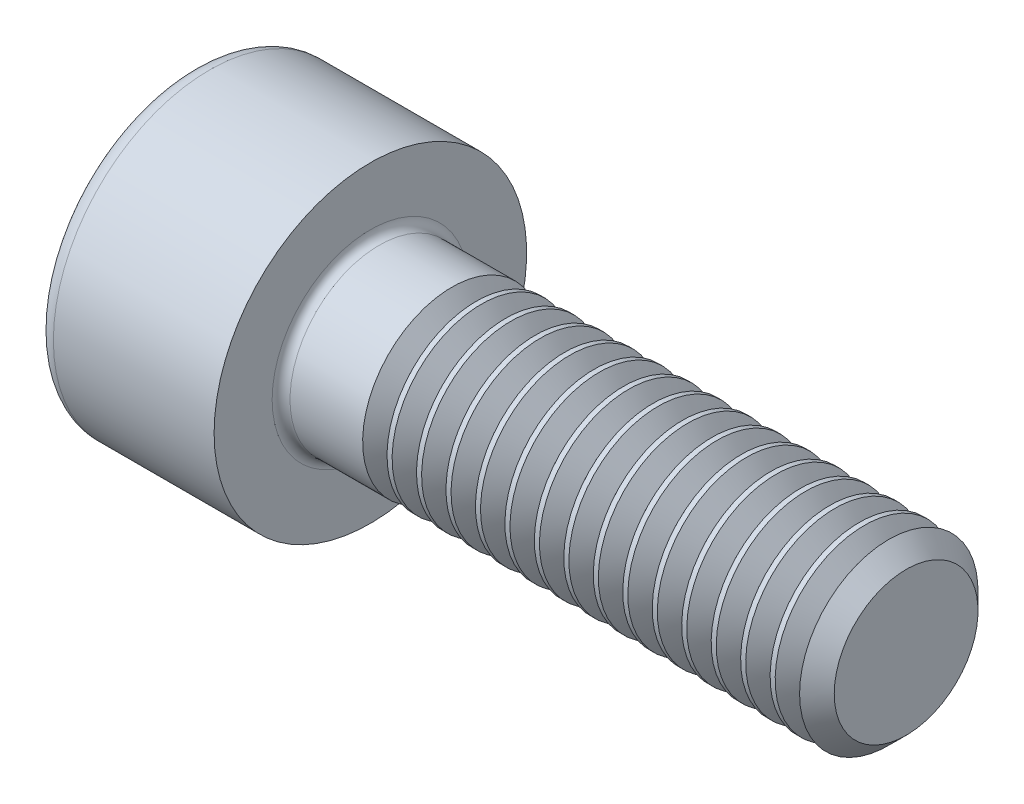
SolidWorks part; units mm, degrees
revolve "Base-Revolve" add sketch "BodySke"
sketch "BodySke" plane through (0, 0, 0) normal (0, 0, 1) x (1, 0, 0)
  line L0 (0, 0) -> (0, 3.5)
  line L1 (0, 3.5) -> (4, 3.5)
  line L2 (4, 3.5) -> (4, 2)
  line L3 (4, 2) -> (15.61, 2)
  line L4 (16, 1.61) -> (16, 0)
  line L5 (16, 0) -> (0, 0)
  line L6 (-31.75, 0) -> (127, 0) construction
  line L8 (16, 1.61) -> (15.61, 2)
  line L10 (16, -1.61) -> (15.61, -2) construction
  line L11 (4.7, 9.525) -> (4.7, 3.175) construction
  line L12 (4, 9.525) -> (4, 3.175) construction
  line L13 (-44, 9.525) -> (-44, 3.175) construction
cosmetic thread "ThreadCosmetic" [suppressed]
fillet "Fillet1" radius 0.2 1 edges at (4, 0, 2)
fillet "Fillet2" radius 0.4 1 edges at (0, 0, 3.5)
ref_plane "Plane1" through (0, 0, 0) normal (0, 0, 1) x (1, 0, 0)
ref_plane "Plane2" through (0, 0, 0) normal (0, 1, 0) x (1, 0, 0)
ref_plane "Plane3" through (0, 0, 0) normal (1, 0, 0) x (0, 0, -1)
sketch "Sketch2" plane through (0, 0, 0) normal (0, 0, 1) x (1, 0, 0)
  line L0 (0, 1.51) -> (2, 1.51)
  line L1 (2, 1.51) -> (2.8718, 0)
  line L2 (-31.75, 0) -> (127, 0) construction
  line L3 (2.8718, 0) -> (0, 0)
  line L4 (0, 0) -> (0, 1.51)
  line L6 (0, 0) -> (47.625, 0) construction
revolve "Hex-PreBroach" cut sketch "Sketch2" angle 360 about L6
sketch "Sketch3" plane through (0, 0, 0) normal (-1, 0, 0) x (0, 0.5, 0.866)
  line L0 (0.8718, 1.51) -> (-0.8718, 1.51)
  line L1 (-0.8718, 1.51) -> (-1.7436, 0)
  line L2 (0.8718, 1.51) -> (1.7436, 0)
  line L3 (0.8718, -1.51) -> (1.7436, 0)
  line L4 (0.8718, -1.51) -> (-0.8718, -1.51)
  line L5 (-0.8718, -1.51) -> (-1.7436, 0)
extrude "Hex" cut sketch "Sketch3" against normal blind 2
sketch "ThdSchSke" plane through (0, 0, 0) normal (0, 0, 1) x (1, 0, 0)
  line L0 (6.1, -1.61) -> (5.8269, -2)
  line L1 (6.1, -1.61) -> (6.3731, -2)
  line L2 (6.3731, -2) -> (6.3731, -2.5)
  line L3 (-3.175, 0) -> (5.1513, 0) construction
  line L4 (0, 3.1) -> (0, -3.1) construction
  line L5 (6.3731, -2.5) -> (5.8269, -2.5)
  line L6 (5.8269, -2.5) -> (5.8269, -2)
revolve "ThreadSchematic" cut sketch "ThdSchSke" angle 360 about L3
pattern_linear "ThdSchPat" count 15 spacing 0.66 along (1, 0, 0) of "ThreadSchematic"
equation "\"D2@Sketch3\" = \"Hex_size@Sketch3\" / 2"
equation "\"D1@Sketch3\" = \"Hex_size@Sketch3\" / 2"
equation "\"D1@Sketch2\" = \"Hex_size@Sketch3\" / 2"
equation "\"Thread_minor@ThreadCosmetic\"  =  \"Minor_dia@BodySke\""
equation "\"Depth@Sketch2\" =  \"Key_eng@Hex\""
equation "\"Thread_length@ThreadCosmetic\" = ((sgn( (\"Length@BodySke\" - \"Advance@BodySke\" * 3.0) - \"Thread_nom@BodySke\" )-1)*( (\"Length@BodySke\" - \"Advance@BodySke\" * 3.0) - \"Thread_nom@BodySke\" ))/-2+ \"Thread_nom@BodySke\""
equation "\"Thread_minor@ThdSchSke\" = \"Minor_dia@BodySke\""
equation "\"Diameter@ThdSchSke\" = \"Diameter@BodySke\""
equation "\"Overcut@ThdSchSke\" = \"Diameter@BodySke\" * 1.25"
equation "\"Start@ThdSchSke\" = \"Head_ht@BodySke\" + \"Length@BodySke\" - \"Thread_length@ThreadCosmetic\"  '---Non-countersunk---"
equation "\"Num_threads@ThdSchPat\" = int( \"Thread_length@ThreadCosmetic\" / \"Advance@BodySke\" + 0.999 )  + 1"
equation "\"Advance@ThdSchPat\" = \"Thread_length@ThreadCosmetic\" /  (\"Num_threads@ThdSchPat\" - 1) 'relax it"
equation "\"Num_threads@ThdSchPat\" = \"Num_threads@ThdSchPat\" - sgn( \"Num_threads@ThdSchPat\" - 1) '---chamfered tips only---"
